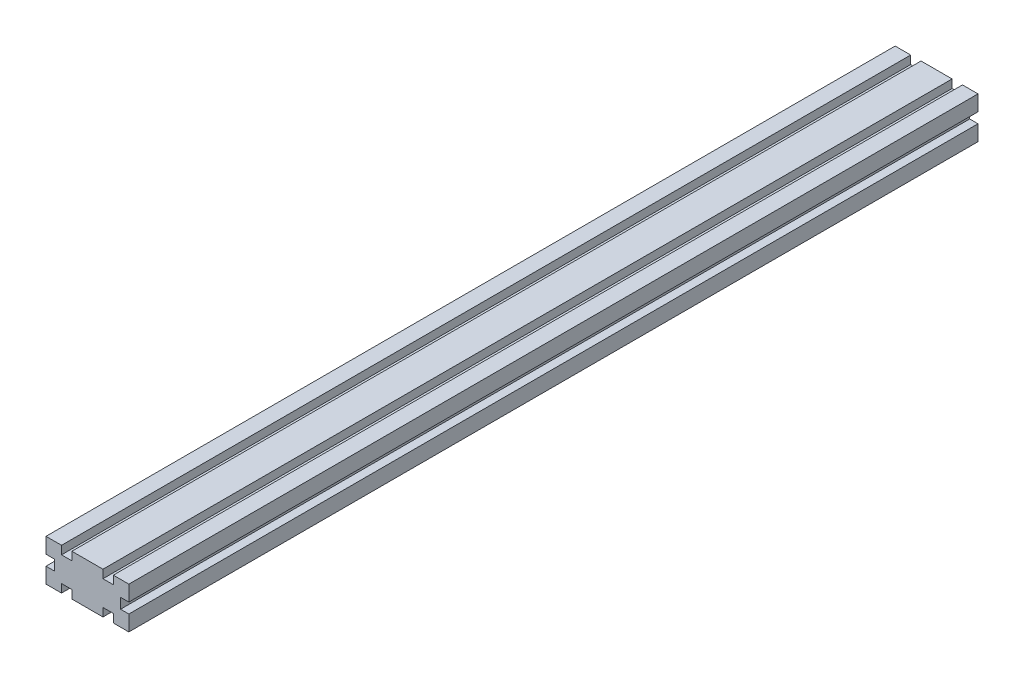
SolidWorks part; units mm, degrees
ref_plane "Plan de face" through (0, 0, 0) normal (0, 0, 1) x (1, 0, 0)
ref_plane "Plan de dessus" through (0, 0, 0) normal (0, 1, 0) x (1, 0, 0)
ref_plane "Plan de droite" through (0, 0, 0) normal (1, 0, 0) x (0, 0, -1)
sketch "Esquisse1" plane through (0, 0, 0) normal (0, 0, 1) x (1, 0, 0)
  line L0 (20, 20) -> (20, 0)
  line L1 (0, 0) -> (40, 0)
  line L2 (0, 0) -> (0, 20)
  line L3 (0, 20) -> (40, 20)
  line L4 (40, 0) -> (40, 20)
  line L5 (20, 0) -> (40, 20)
  line L6 (40, 0) -> (20, 20)
  line L7 (0, 0) -> (20, 20)
  line L8 (20, 0) -> (0, 20)
  line L10 (4, 4) -> (16, 4)
  line L11 (4, 4) -> (4, 16)
  line L12 (4, 16) -> (16, 16)
  line L13 (16, 4) -> (16, 16)
  line L14 (4, 4) -> (16, 16) construction
  line L15 (4, 16) -> (16, 4) construction
  line L16 (24, 4) -> (36, 4)
  line L17 (24, 4) -> (24, 16)
  line L18 (24, 16) -> (36, 16)
  line L19 (36, 4) -> (36, 16)
  line L20 (24, 4) -> (36, 16) construction
  line L21 (24, 16) -> (36, 4) construction
  line L22 (12.5, 0) -> (7.5, 0)
  line L23 (12.5, 0) -> (12.5, 20)
  line L24 (12.5, 20) -> (7.5, 20)
  line L25 (7.5, 0) -> (7.5, 20)
  line L26 (12.5, 0) -> (7.5, 20) construction
  line L27 (12.5, 20) -> (7.5, 0) construction
  line L28 (32.5, 0) -> (27.5, 0)
  line L29 (32.5, 0) -> (32.5, 20)
  line L30 (32.5, 20) -> (27.5, 20)
  line L31 (27.5, 0) -> (27.5, 20)
  line L32 (32.5, 0) -> (27.5, 20) construction
  line L33 (32.5, 20) -> (27.5, 0) construction
  line L34 (0, 7.5) -> (40, 7.5)
  line L35 (0, 7.5) -> (0, 12.5)
  line L36 (0, 12.5) -> (40, 12.5)
  line L37 (40, 7.5) -> (40, 12.5)
  line L38 (0, 7.5) -> (40, 12.5) construction
  line L39 (0, 12.5) -> (40, 7.5) construction
  point P7 (10, 10)
  point P12 (30, 10)
  point P17 (10, 10)
  point P22 (30, 10)
  point P27 (20, 10)
  dimension "D1" = 20
  dimension "D2" = 40
  dimension "D3" = 12
  dimension "D5" = 5
  dimension "D6" = 5
  dimension "D7" = 5
extrude "Boss.-Extru.1" add sketch "Esquisse1" along normal blind 410 contours L12 L25 L3 L8 | L2 L36 L11 L8 | L34 L2 L7 L11 | L1 L25 L10 L7 | L34 L11 L7 | L10 L25 L7 | L11 L36 L8 | L8 L25 L12 | L36 L11 L34 L25 | L25 L7 L8 | L36 L8 L7 | L8 L23 L7 | L7 L34 L8 | L23 L10 L8 | L34 L8 L13 | L34 L13 L8 L0 | L25 L36 L23 L12 | L36 L23 L34 L13 | L23 L7 L12 | L23 L12 L7 L3 | L7 L36 L13 | L13 L36 L0 L7 | L23 L1 L8 L10 | L34 L25 L10 L23 | L36 L13 L34 L0 | L36 L0 L34 L17 | L0 L36 L17 L6 | L18 L31 L3 L6 | L17 L36 L6 | L6 L31 L18 | L36 L17 L34 L31 | L34 L17 L5 | L34 L0 L5 L17 | L1 L31 L16 L5 | L16 L31 L5 | L34 L31 L16 L29 | L29 L16 L6 | L34 L6 L19 | L34 L19 L6 L4 | L29 L1 L6 L16 | L36 L29 L34 L19 | L6 L29 L5 | L5 L34 L6 | L31 L5 L6 | L36 L6 L5 | L5 L36 L19 | L29 L5 L18 | L29 L18 L5 L3 | L19 L36 L4 L5 | L31 L36 L29 L18
